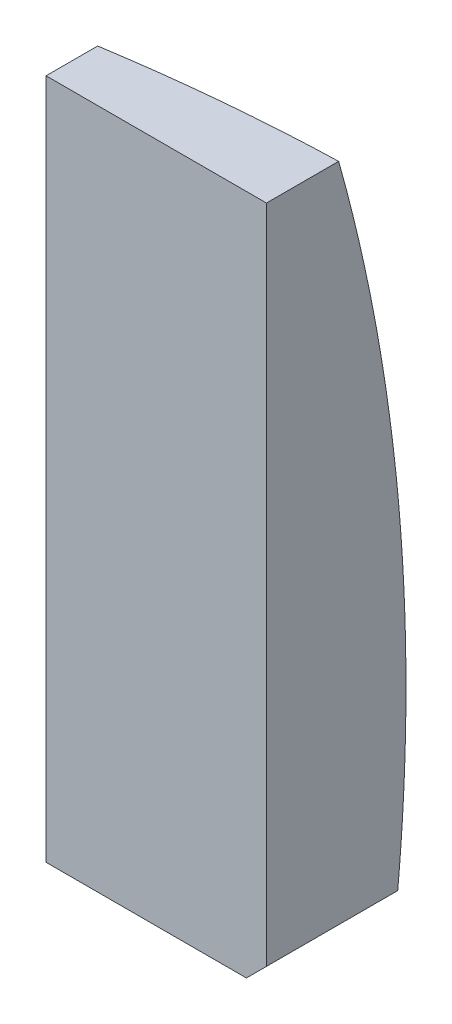
SolidWorks part; units mm, degrees
material "Стекло"
ref_plane "Спереди" through (0, 0, 0) normal (0, 0, 1) x (1, 0, 0)
ref_plane "Сверху" through (0, 0, 0) normal (0, 1, 0) x (1, 0, 0)
ref_plane "Справа" through (0, 0, 0) normal (1, 0, 0) x (0, 0, -1)
sketch "Эскиз1" plane through (0, 0, 0) normal (0, 1, 0) x (1, 0, 0)
  line L0 (0, 3.5) -> (0, 0) construction
  line L1 (0, 3.5) -> (18, 3.5) construction
  line L2 (14, 0) -> (14, 1.2767)
  line L3 (0, 0) -> (14, 0)
  line L4 (0, 3.5) -> (0, 0)
  arc A0 (0, 3.5) -> (14, 1.2767) centre (0, -41.69) cw
  dimension "D3" = 45.19
  dimension "D1" = 3.5
  dimension "D2" = 14
revolve "Повернуть1" add sketch "Эскиз1" angle 360 about L4
sketch "Эскиз2" plane through (0, 0, 0) normal (0, 0, 1) x (1, 0, 0)
  line L0 (0, 14) -> (0, -14) construction
  line L1 (1.3, 12.2) -> (6.8, 12.2)
  line L2 (1.3, 12.2) -> (1.3, -4.8)
  line L3 (1.3, -4.8) -> (6.8, -4.8)
  line L4 (6.8, 12.2) -> (6.8, -4.8)
  line L5 (-6.8, 12.2) -> (-6.8, -4.8)
  line L6 (-1.3, -4.8) -> (-6.8, -4.8)
  line L7 (-1.3, 12.2) -> (-1.3, -4.8)
  line L8 (-1.3, 12.2) -> (-6.8, 12.2)
  circle A0 centre (0, 0) radius 14 construction
  point P4 (3.3, 2.7)
  dimension "D1" = 5.5
  dimension "D2" = 17
  dimension "D3" = 2.7
  dimension "D4" = 3.3
  dimension "D5" = 2
  dimension "D6" = 7.5
extrude "Вырез-Вытянуть1" cut sketch "Эскиз2" against normal through all flip side to cut contours L7 L8 L5 L6
chamfer "Фаска2" [suppressed] distance 0.25 angle 45
chamfer "Фаска3" distance 0.5 angle 45 1 edges at (-1.3, -4.8, -1.6128)
